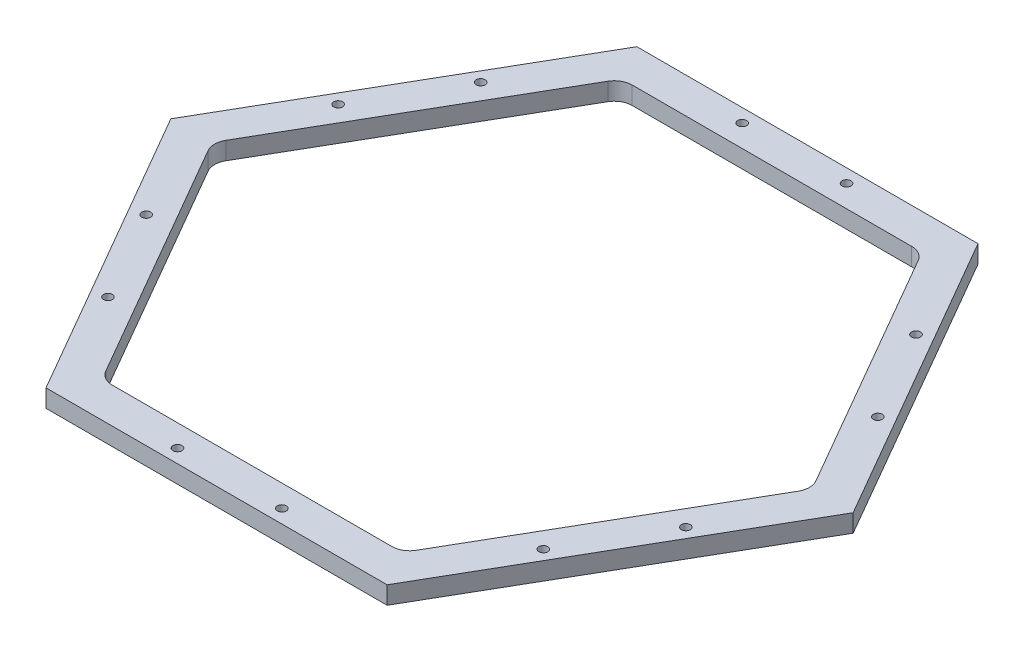
SolidWorks part; units mm, degrees
material "1060 Alloy"
ref_plane "Front Plane" through (0, 0, 0) normal (0, 0, 1) x (1, 0, 0)
ref_plane "Top Plane" through (0, 0, 0) normal (0, 1, 0) x (1, 0, 0)
ref_plane "Right Plane" through (0, 0, 0) normal (1, 0, 0) x (0, 0, -1)
sketch "Sketch1" plane through (0, 0, 0) normal (0, 1, 0) x (1, 0, 0)
  line L0 (60.9985, 0) -> (30.4993, 52.8263)
  line L1 (52.7496, 1.5875) -> (27.7496, 44.8888)
  line L2 (25, 46.4763) -> (-25, 46.4763)
  line L3 (-27.7496, 44.8888) -> (-52.7496, 1.5875)
  line L4 (-52.7496, -1.5875) -> (-27.7496, -44.8888)
  line L5 (-25, -46.4763) -> (25, -46.4763)
  line L6 (27.7496, -44.8888) -> (52.7496, -1.5875)
  line L7 (30.4993, 52.8263) -> (-30.4993, 52.8263)
  line L8 (-30.4993, 52.8263) -> (-60.9985, 0)
  line L9 (-60.9985, 0) -> (-30.4993, -52.8263)
  line L10 (-30.4993, -52.8263) -> (30.4993, -52.8263)
  line L11 (30.4993, -52.8263) -> (60.9985, 0)
  line L12 (-26.8331, 46.4763) -> (-53.6662, 0) construction
  line L13 (-53.6662, 0) -> (-26.8331, -46.4763) construction
  line L14 (-26.8331, -46.4763) -> (26.8331, -46.4763) construction
  line L15 (26.8331, -46.4763) -> (53.6662, 0) construction
  line L16 (53.6662, 0) -> (26.8331, 46.4763) construction
  line L17 (26.8331, 46.4763) -> (-26.8331, 46.4763) construction
  circle A0 centre (0, 0) radius 46.4763 construction
  arc A1 (-52.7496, 1.5875) -> (-52.7496, -1.5875) centre (-50, 0) ccw
  arc A2 (-27.7496, -44.8888) -> (-25, -46.4763) centre (-25, -43.3013) ccw
  arc A3 (25, -46.4763) -> (27.7496, -44.8888) centre (25, -43.3013) ccw
  arc A4 (52.7496, 1.5875) -> (52.7496, -1.5875) centre (50, 0) cw
  arc A5 (27.7496, 44.8888) -> (25, 46.4763) centre (25, 43.3013) ccw
  arc A6 (-25, 46.4763) -> (-27.7496, 44.8888) centre (-25, 43.3013) ccw
  dimension "D2" = 3.175
  dimension "D3" = 50
  dimension "D1" = 6.35
extrude "Boss-Extrude1" add sketch "Sketch1" along normal blind 3.175
hole_wizard "M2x0.4 Tapped Hole1" positions "Sketch3" profile "Sketch2" tap size "M2x0.4" standard "ANSI Metric"
sketch "Sketch3" plane through (0, 3.175, 0) normal (0, 1, 0) x (1, 0, 0)
  point P0 (9.4084, 50.4102)
  point P3 (-9.2543, 50.4102)
sketch "Sketch2" plane through (9.4084, 3.175, -50.4102) normal (1, 0, 0) x (0, 0, 1)
  line L0 (0, 0) -> (0, 6.5767)
  line L1 (0, 6.5767) -> (0.8, 6.096)
  line L2 (0.8, 6.096) -> (0.8, 0)
  line L5 (0.8, 0) -> (0, 0)
  line L10 (0, 6.5767) -> (-0.8, 6.096) construction
  line L11 (0, -6.35) -> (0, 107.95) construction
  dimension "Tap Drill Dia." = 1.6
  dimension "Tap Drill Depth" = 6.096
  dimension "Drill Angle" = 118
cosmetic thread "Hole Thread1" parameters "D1"=3.175, "D2"=2
cosmetic thread "Hole Thread2" parameters "D1"=3.175, "D2"=2
pattern_circular "CirPattern1" count 6 over 360 about axis through (0, 0, 0) along (0, 1, 0) of "M2x0.4 Tapped Hole1"
